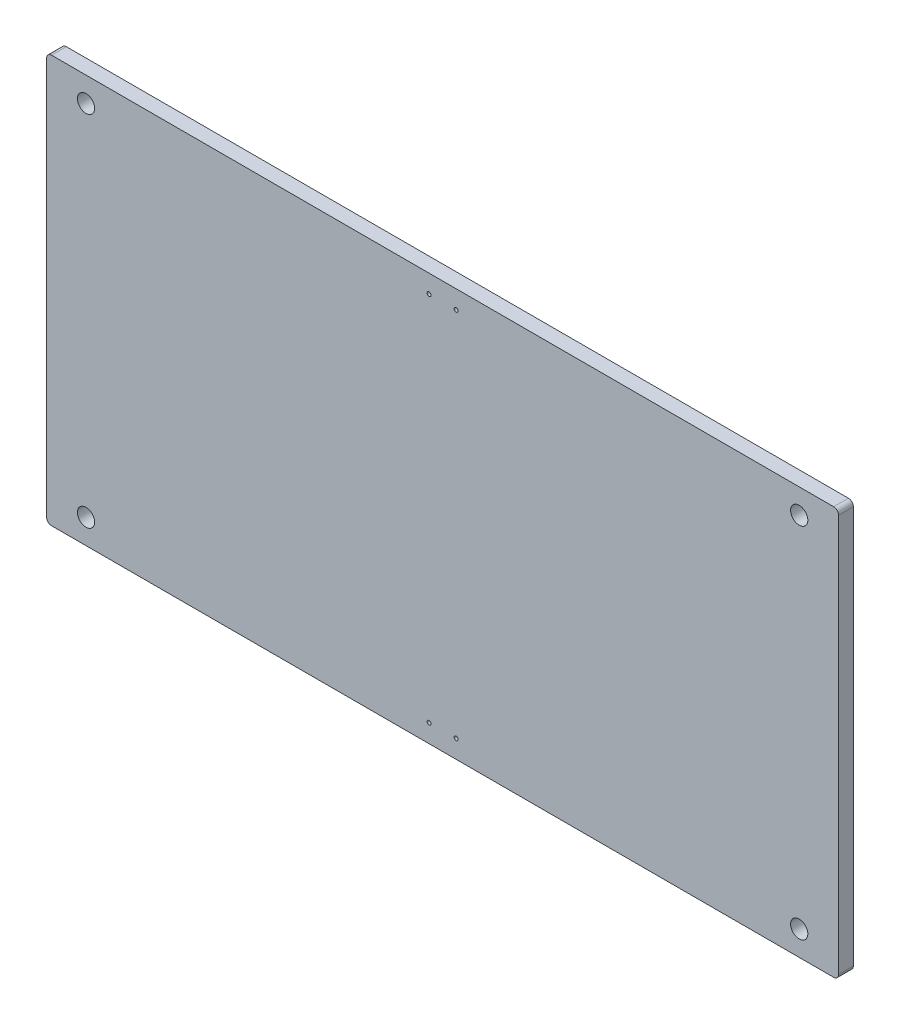
SolidWorks part; units mm, degrees
ref_plane "Front Plane" through (0, 0, 0) normal (0, 0, 1) x (1, 0, 0)
ref_plane "Top Plane" through (0, 0, 0) normal (0, 1, 0) x (1, 0, 0)
ref_plane "Right Plane" through (0, 0, 0) normal (1, 0, 0) x (0, 0, -1)
sketch "Sketch1" plane through (0, 0, 0) normal (0, 0, 1) x (1, 0, 0)
  line L0 (591.9925, 431.4754) -> (591.9925, 265.8654) construction
  line L1 (431.0875, 431.4754) -> (752.8975, 431.4754)
  line L2 (431.0875, 431.4754) -> (431.0875, 265.8654)
  line L3 (431.0875, 265.8654) -> (752.8975, 265.8654)
  line L4 (752.8975, 431.4754) -> (752.8975, 265.8654)
  dimension "D1" = 321.81
  dimension "D2" = 165.61
extrude "Boss-Extrude1" add sketch "Sketch1" along normal blind 6
sketch "Sketch3" plane through (0, 0, 6) normal (0, 0, 1) x (1, 0, 0)
  line L0 (752.8975, 431.4754) -> (431.0875, 431.4754) construction
  line L1 (431.0875, 265.8654) -> (752.8975, 265.8654) construction
  line L2 (431.0875, 431.4754) -> (431.0875, 265.8654) construction
  line L3 (752.8975, 265.8654) -> (752.8975, 431.4754) construction
  circle A0 centre (447.0875, 421.4754) radius 3.5
  circle A1 centre (736.8975, 421.4754) radius 3.5
  circle A2 centre (736.8975, 275.8654) radius 3.5
  circle A3 centre (447.0875, 275.8654) radius 3.5
  dimension "D1" = 7
  dimension "D2" = 7
  dimension "D3" = 7
  dimension "D4" = 7
  dimension "D5" = 10
  dimension "D6" = 10
  dimension "D7" = 16
  dimension "D8" = 16
extrude "Cut-Extrude1" cut sketch "Sketch3" against normal through all
sketch "Sketch4" [suppressed] plane through (0, 0, 6) normal (0, 0, 1) x (1, 0, 0)
  circle A0 centre (467.0875, 421.4754) radius 3.9
  circle A1 centre (716.8975, 421.4754) radius 3.9
  circle A2 centre (716.8975, 275.8654) radius 3.9
  circle A3 centre (467.0875, 275.8654) radius 3.9
  circle A5 centre (736.8975, 421.4754) radius 3.5 construction
  point P8 (447.0875, 421.4754)
  point P9 (447.0875, 275.8654)
  dimension "D1" = 7.8
  dimension "D2" = 7.8
  dimension "D3" = 7.8
  dimension "D4" = 7.8
  dimension "D7" = 20
  dimension "D5" = 20
extrude "Cut-Extrude2" [suppressed] cut sketch "Sketch4" against normal blind 10
sketch "Sketch5" plane through (0, 0, 6) normal (0, 0, 1) x (1, 0, 0)
  line L0 (581.9925, 421.4754) -> (601.9925, 421.4754) construction
  line L1 (591.9925, 431.4754) -> (591.9925, 265.8654) construction
  line L2 (431.0875, 265.8654) -> (752.8975, 265.8654) construction
  line L3 (752.8975, 431.4754) -> (431.0875, 431.4754) construction
  circle A0 centre (581.9925, 421.4754) radius 2.5
  circle A1 centre (601.9925, 421.4754) radius 2.5
  circle A2 centre (581.9925, 275.8654) radius 2.5
  circle A3 centre (601.9925, 275.8654) radius 2.5
  point P2 (591.9925, 421.4754)
  dimension "D6" = 10
  dimension "D1" = 5
  dimension "D2" = 5
  dimension "D4" = 5
  dimension "D5" = 5
  dimension "D3" = 20
  dimension "D7" = 10
extrude "Cut-Extrude4" [suppressed] cut sketch "Sketch5" against normal blind 10
sketch "Sketch6" plane through (0, 0, 6) normal (0, 0, 1) x (1, 0, 0)
  line L0 (431.0875, 431.4754) -> (752.8975, 431.4754) construction
  line L1 (431.0875, 265.8654) -> (752.8975, 265.8654) construction
  line L2 (586.4925, 424.0754) -> (597.4925, 424.0754) construction
  line L3 (591.9925, 431.4754) -> (591.9925, 265.8654) construction
  circle A0 centre (586.4925, 424.0754) radius 0.8
  circle A1 centre (597.4925, 424.0754) radius 0.8
  circle A2 centre (586.4925, 273.2654) radius 0.8
  circle A3 centre (597.4925, 273.2654) radius 0.8
  point P12 (591.9925, 424.0754)
  dimension "D3" = 1.6
  dimension "D4" = 1.6
  dimension "D5" = 1.6
  dimension "D6" = 1.6
  dimension "D1" = 7.4
  dimension "D2" = 11
  dimension "D7" = 7.4
extrude "Cut-Extrude5" cut sketch "Sketch6" against normal blind 10
fillet "Fillet1" radius 2 4 edges at (752.8975, 431.4754, 3) (752.8975, 265.8654, 3) (431.0875, 265.8654, 3) (431.0875, 431.4754, 3)
equation "\"D2@Sketch4\"=\"D1@Sketch4\""
equation "\"D3@Sketch4\"=\"D1@Sketch4\""
equation "\"D4@Sketch4\"=\"D1@Sketch4\""
equation "\"D7@Sketch4\"=\"D5@Sketch4\""
equation "\"D2@Sketch3\"=\"D1@Sketch3\""
equation "\"D3@Sketch3\"=\"D1@Sketch3\""
equation "\"D4@Sketch3\"=\"D1@Sketch3\""
equation "\"D6@Sketch3\"=\"D5@Sketch3\""
equation "\"D8@Sketch3\"=\"D7@Sketch3\""
equation "\"D4@Sketch5\"=\"D1@Sketch5\""
equation "\"D5@Sketch5\"=\"D1@Sketch5\""
equation "\"D2@Sketch5\"=\"D1@Sketch5\""
equation "\"D6@Sketch5\"=\"D7@Sketch5\""
equation "\"D4@Sketch6\"=\"D3@Sketch6\""
equation "\"D5@Sketch6\"=\"D3@Sketch6\""
equation "\"D6@Sketch6\"=\"D3@Sketch6\""
equation "\"D7@Sketch6\"=\"D1@Sketch6\""
